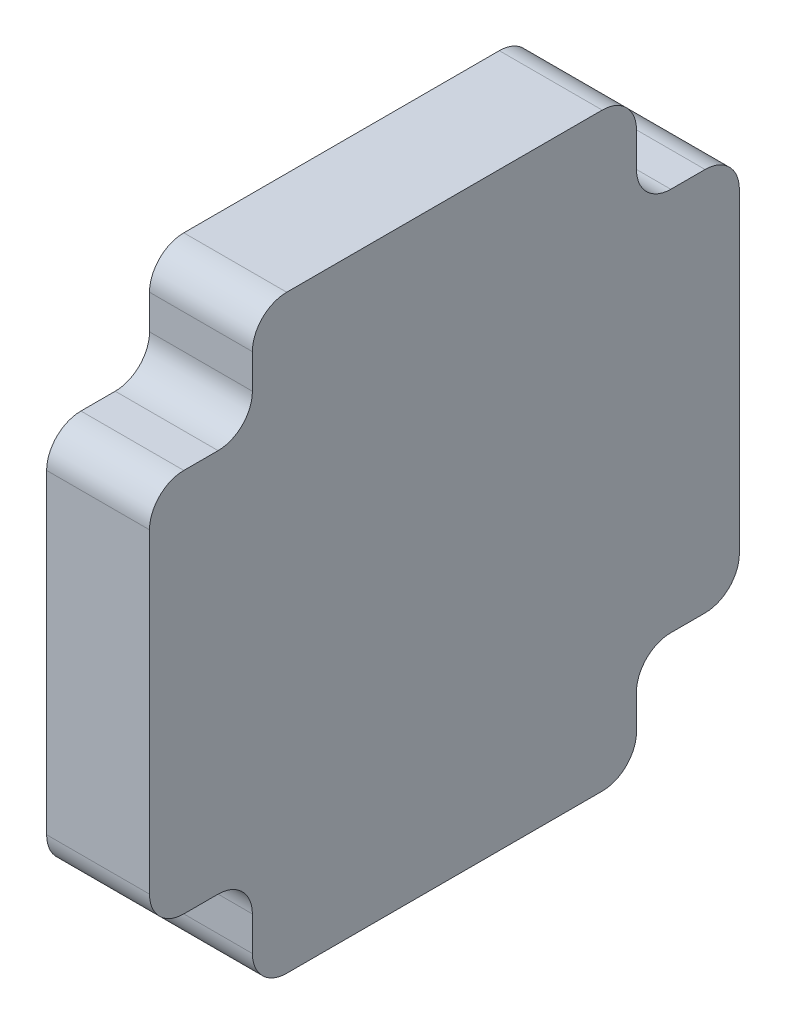
SolidWorks part; units mm, degrees
ref_plane "Front Plane" through (0, 0, 0) normal (0, 0, 1) x (1, 0, 0)
ref_plane "Top Plane" through (0, 0, 0) normal (0, 1, 0) x (1, 0, 0)
ref_plane "Right Plane" through (0, 0, 0) normal (1, 0, 0) x (0, 0, -1)
sketch "Sketch1" plane through (0, 0, 0) normal (1, 0, 0) x (0, 0, -1)
  line L0 (2.3431, 83.6569) -> (83.6569, 2.3431) construction
  line L1 (20, 0) -> (66, 0)
  line L2 (0, 20) -> (0, 66)
  line L3 (20, 86) -> (66, 86)
  line L4 (86, 20) -> (86, 66)
  line L5 (2.3431, 2.3431) -> (83.6569, 83.6569) construction
  line L6 (5, 71) -> (10, 71)
  line L7 (15, 76) -> (15, 81)
  line L8 (76, 15) -> (81, 15)
  line L9 (71, 5) -> (71, 10)
  line L10 (71, 81) -> (71, 76)
  line L11 (76, 71) -> (81, 71)
  line L12 (15, 10) -> (15, 5)
  line L14 (5, 15) -> (10, 15)
  arc A0 (5, 15) -> (0, 20) centre (5, 20) cw
  arc A1 (15, 5) -> (20, 0) centre (20, 5) ccw
  arc A2 (15, 10) -> (10, 15) centre (10, 10) ccw
  arc A3 (71, 5) -> (66, 0) centre (66, 5) cw
  arc A4 (81, 15) -> (86, 20) centre (81, 20) ccw
  arc A5 (76, 15) -> (71, 10) centre (76, 10) ccw
  arc A6 (81, 71) -> (86, 66) centre (81, 66) cw
  arc A7 (71, 76) -> (76, 71) centre (76, 76) ccw
  arc A8 (71, 81) -> (66, 86) centre (66, 81) ccw
  arc A9 (15, 81) -> (20, 86) centre (20, 81) cw
  arc A10 (10, 71) -> (15, 76) centre (10, 76) ccw
  arc A11 (5, 71) -> (0, 66) centre (5, 66) ccw
  point P3 (0, 15)
  point P7 (86, 86)
  point P9 (15, 0)
  point P12 (0, 0)
  point P15 (0, 86)
  point P30 (15, 15)
  point P33 (71, 0)
  point P36 (86, 15)
  point P39 (71, 15)
  point P42 (86, 71)
  point P45 (71, 71)
  point P48 (71, 86)
  point P51 (15, 86)
  point P54 (15, 71)
  point P57 (0, 71)
  dimension "D2" = 5
  dimension "D1" = 86
  dimension "D3" = 15
extrude "Boss-Extrude1" add sketch "Sketch1" along normal blind 15
